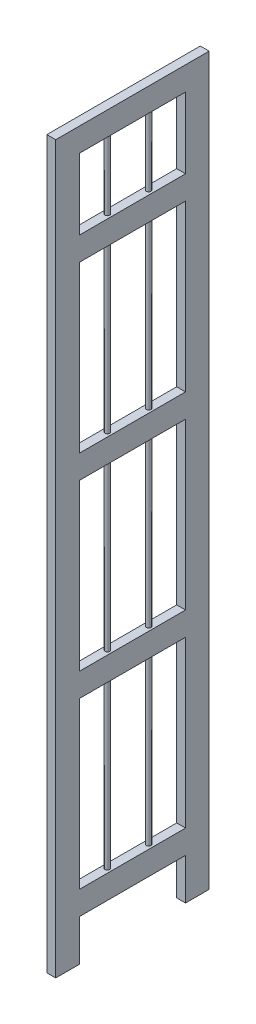
SolidWorks part; units mm, degrees
material "柚木"
ref_plane "前视基准面" through (0, 0, 0) normal (0, 0, 1) x (1, 0, 0)
ref_plane "上视基准面" through (0, 0, 0) normal (0, 1, 0) x (1, 0, 0)
ref_plane "右视基准面" through (0, 0, 0) normal (1, 0, 0) x (0, 0, -1)
sketch "草图1" plane through (0, 0, 0) normal (1, 0, 0) x (0, 0, -1)
  line L0 (-90, 0) -> (-90, 1190)
  line L1 (-130, 0) -> (130, 0) construction
  line L2 (-130, 0) -> (-130, 1230)
  line L3 (-130, 1230) -> (130, 1230)
  line L4 (130, 0) -> (130, 1230)
  line L5 (-90, 1190) -> (90, 1190)
  line L6 (90, 0) -> (90, 1190)
  line L7 (-90, 40) -> (-90, 1190) construction
  line L8 (-90, 40) -> (90, 40) construction
  line L9 (90, 40) -> (90, 1190) construction
  line L10 (-130, 0) -> (130, 0) construction
  line L11 (-130, 0) -> (-90, 0)
  line L12 (90, 0) -> (130, 0)
  dimension "D1" = 1230
  dimension "D2" = 260
  dimension "D3" = 40
extrude "凸台-拉伸1" add sketch "草图1" against normal blind 15
sketch "草图2" plane through (0, 0, 0) normal (1, 0, 0) x (0, 0, -1)
  line L1 (-90, 110) -> (90, 110)
  line L2 (-90, 110) -> (-90, 70)
  line L3 (-90, 70) -> (90, 70)
  line L4 (90, 110) -> (90, 70)
  line L6 (-90, 0) -> (-90, 1190) construction
  line L7 (90, 1190) -> (90, 0) construction
  line L8 (-130, 0) -> (-90, 0) construction
  point P8 (-110, 0)
  point P11 (-110, 0)
  dimension "D1" = 40
  dimension "D2" = 180
  dimension "D3" = 110
extrude "凸台-拉伸2" add sketch "草图2" against normal up to surface (15 mm away) up to face at (-15, 605, 0)
pattern_linear "阵列(线性)1" count 4 spacing 320 along (0, 1, 0) of "凸台-拉伸2"
sketch "草图3" plane through (0, 110, 0) normal (0, 1, 0) x (1, 0, 0)
  line L0 (0, 0) -> (-15, 0) construction
  line L1 (0, 90) -> (0, -90) construction
  line L2 (-15, -90) -> (-15, 90) construction
  line L3 (-7.5, 0) -> (-7.5, -35) construction
  circle A0 centre (-7.5, -35) radius 4
  point P9 (-167.099, -222.9628)
  dimension "D1" = 8
  dimension "D2" = 70
extrude "凸台-拉伸3" add sketch "草图3" along normal up to surface (1080 mm away) up to face at (-7.5, 1190, 0)
mirror "镜向1" about plane through (0, 0, 0) normal (0, 0, 1) of "凸台-拉伸3"
